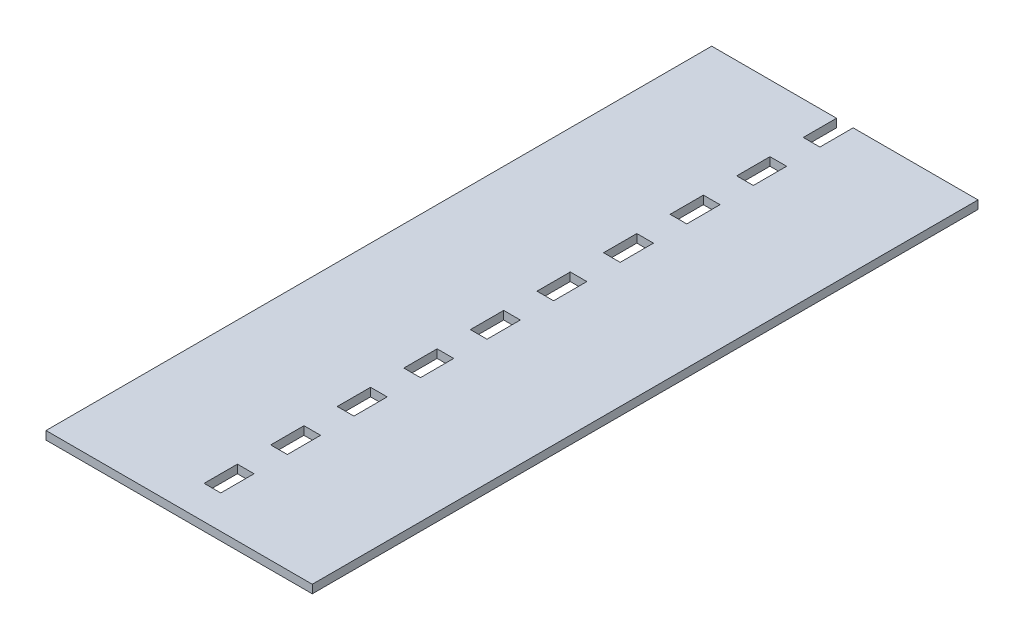
SolidWorks part; units mm, degrees
material "Gray Cast Iron"
ref_plane "Front Plane" through (0, 0, 0) normal (0, 0, 1) x (1, 0, 0)
ref_plane "Top Plane" through (0, 0, 0) normal (0, 1, 0) x (1, 0, 0)
ref_plane "Right Plane" through (0, 0, 0) normal (1, 0, 0) x (0, 0, -1)
sketch "Sketch1" plane through (0, 0, 0) normal (0, 1, 0) x (1, 0, 0)
  line L0 (-57.9626, 1946.8475) -> (-57.9626, 1846.8475) construction
  line L2 (-457.9626, 1946.8475) -> (-457.9626, -53.1525)
  line L3 (-457.9626, -53.1525) -> (342.0374, -53.1525)
  line L4 (342.0374, 1946.8475) -> (342.0374, -53.1525)
  line L5 (-32.9626, 1846.8475) -> (-82.9626, 1846.8475)
  line L6 (-82.9626, 1846.8475) -> (-82.9626, 1946.8475)
  line L7 (-32.9626, 1846.8475) -> (-32.9626, 1946.8475)
  line L8 (-457.9626, 1946.8475) -> (-82.9626, 1946.8475)
  line L9 (342.0374, 1946.8475) -> (-32.9626, 1946.8475)
  line L10 (-32.9626, 1946.8475) -> (-82.9626, 1946.8475)
  line L11 (-32.9626, 1646.8475) -> (-32.9626, 1746.8475)
  line L12 (-82.9626, 1646.8475) -> (-82.9626, 1746.8475)
  line L13 (-32.9626, 1646.8475) -> (-82.9626, 1646.8475)
  line L14 (-32.9626, 1746.8475) -> (-82.9626, 1746.8475)
  line L15 (-32.9626, 1446.8475) -> (-32.9626, 1546.8475)
  line L16 (-82.9626, 1446.8475) -> (-82.9626, 1546.8475)
  line L17 (-32.9626, 1446.8475) -> (-82.9626, 1446.8475)
  line L18 (-32.9626, 1546.8475) -> (-82.9626, 1546.8475)
  line L19 (-32.9626, 1246.8475) -> (-32.9626, 1346.8475)
  line L20 (-82.9626, 1246.8475) -> (-82.9626, 1346.8475)
  line L21 (-32.9626, 1246.8475) -> (-82.9626, 1246.8475)
  line L22 (-32.9626, 1346.8475) -> (-82.9626, 1346.8475)
  line L23 (-32.9626, 1046.8475) -> (-32.9626, 1146.8475)
  line L24 (-82.9626, 1046.8475) -> (-82.9626, 1146.8475)
  line L25 (-32.9626, 1046.8475) -> (-82.9626, 1046.8475)
  line L26 (-32.9626, 1146.8475) -> (-82.9626, 1146.8475)
  line L27 (-32.9626, 846.8475) -> (-32.9626, 946.8475)
  line L28 (-82.9626, 846.8475) -> (-82.9626, 946.8475)
  line L29 (-32.9626, 846.8475) -> (-82.9626, 846.8475)
  line L30 (-32.9626, 946.8475) -> (-82.9626, 946.8475)
  line L31 (-32.9626, 646.8475) -> (-32.9626, 746.8475)
  line L32 (-82.9626, 646.8475) -> (-82.9626, 746.8475)
  line L33 (-32.9626, 646.8475) -> (-82.9626, 646.8475)
  line L34 (-32.9626, 746.8475) -> (-82.9626, 746.8475)
  line L35 (-32.9626, 446.8475) -> (-32.9626, 546.8475)
  line L36 (-82.9626, 446.8475) -> (-82.9626, 546.8475)
  line L37 (-32.9626, 446.8475) -> (-82.9626, 446.8475)
  line L38 (-32.9626, 546.8475) -> (-82.9626, 546.8475)
  line L39 (-32.9626, 246.8475) -> (-32.9626, 346.8475)
  line L40 (-82.9626, 246.8475) -> (-82.9626, 346.8475)
  line L41 (-32.9626, 246.8475) -> (-82.9626, 246.8475)
  line L42 (-32.9626, 346.8475) -> (-82.9626, 346.8475)
  line L43 (-32.9626, 46.8475) -> (-32.9626, 146.8475)
  line L44 (-82.9626, 46.8475) -> (-82.9626, 146.8475)
  line L45 (-32.9626, 46.8475) -> (-82.9626, 46.8475)
  line L46 (-32.9626, 146.8475) -> (-82.9626, 146.8475)
  line L47 (-32.9626, -153.1525) -> (-32.9626, -53.1525)
  line L48 (-82.9626, -153.1525) -> (-82.9626, -53.1525)
  line L49 (-32.9626, -153.1525) -> (-82.9626, -153.1525)
  line L50 (-32.9626, -53.1525) -> (-82.9626, -53.1525)
  dimension "D1" = 2000
  dimension "D2" = 800
  dimension "D3" = 11
  dimension "D4" = 375
  dimension "D5" = 100
  dimension "D6" = 342.0374
  dimension "D7" = 46.8475
extrude "Boss-Extrude1" add sketch "Sketch1" along normal blind 25 contours L4 L9 L7 L5 L6 L8 L2 L3 L46 L43 L45 L44 L42 L39 L41 L40 L38 L35 L37 L36 L34 L31 L33 L32 L30 L27 L29 L28 L26 L23 L25 L24 L22 L19 L21 L20 L18 L15 L17 L16
